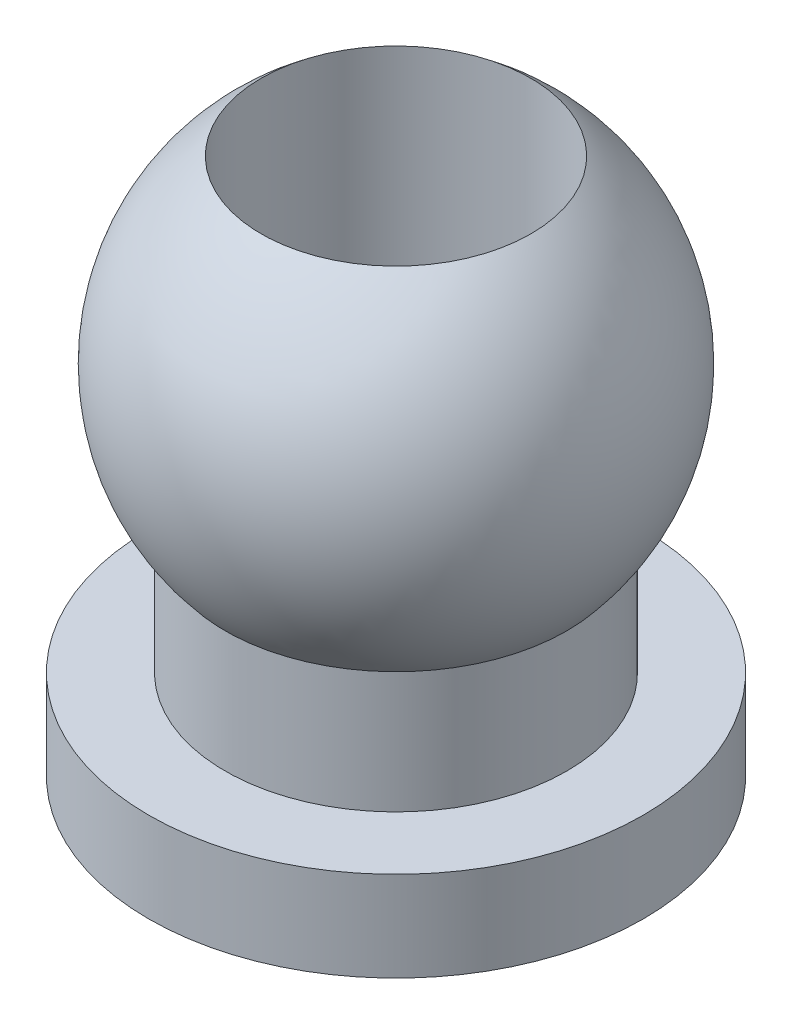
SolidWorks part; units mm, degrees
ref_plane "前基準面" through (0, 0, 0) normal (0, 0, 1) x (1, 0, 0)
ref_plane "上基準面" through (0, 0, 0) normal (0, 1, 0) x (1, 0, 0)
ref_plane "右基準面" through (0, 0, 0) normal (1, 0, 0) x (0, 0, -1)
sketch "草圖1" plane through (0, 0, 0) normal (0, 0, 1) x (1, 0, 0)
  line L0 (0, 2.75) -> (0, -3.9753) construction
  line L1 (0, -3.9753) -> (2.75, -3.9753)
  line L2 (2.75, -3.9753) -> (2.75, -2.9753)
  line L3 (2.75, -2.9753) -> (1.9, -2.9753)
  line L4 (1.9, -2.9753) -> (1.9, -1.6248)
  line L5 (0, 2.0247) -> (1.4665, 2.0247)
  line L6 (0, 2.0247) -> (0, -3.9753)
  arc A0 (1.9, -1.6248) -> (1.4665, 2.0247) centre (0, 0) ccw
  dimension "D1" = 2.5
  dimension "D2" = 6
  dimension "D4" = 1
  dimension "D5" = 1.9
  dimension "D6" = 2.75
revolve "旋轉1" add sketch "草圖1" angle 360 about L0
sketch "草圖3" plane through (0, -3.9753, 0) normal (0, -1, 0) x (1, 0, 0)
  circle A0 centre (0, 0) radius 1.5
extrude "除料-伸長1" cut sketch "草圖3" against normal through all
sketch "草圖4" plane through (0, 0, 0) normal (0, 0, 1) x (1, 0, 0)
  line L0 (0, 0) -> (0, 2) construction
  line L1 (1.5, 2) -> (-1.5, 2) construction
  line L4 (0, 0) -> (2.5, 0) construction
  arc A0 (1.9, -1.6248) -> (1.5, 2) centre (0, 0) ccw construction
